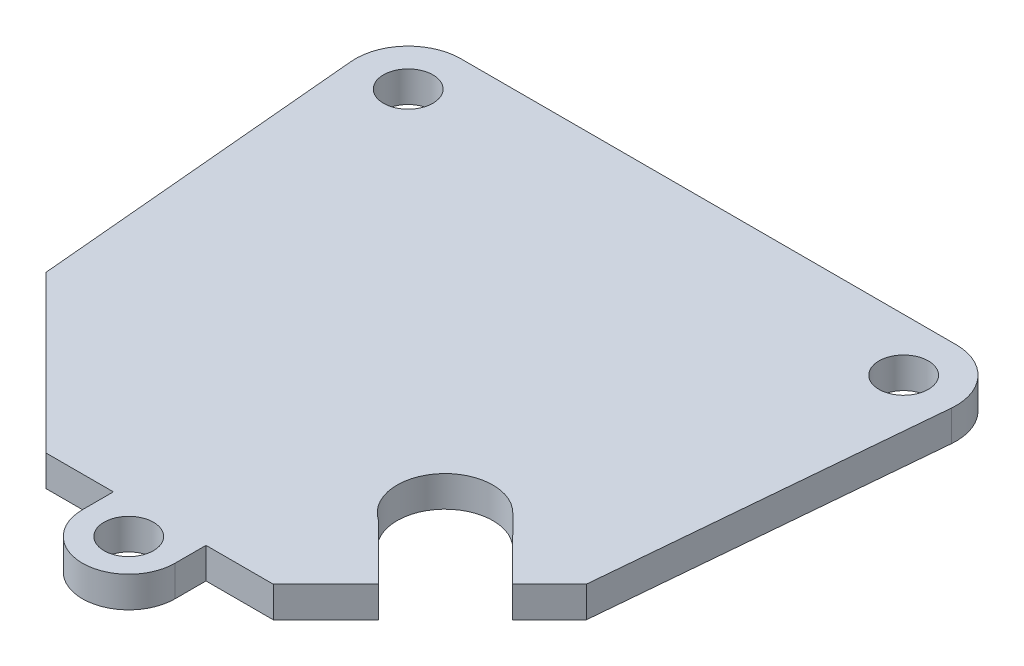
SolidWorks part; units mm, degrees
ref_plane "Front Plane" through (0, 0, 0) normal (0, 0, 1) x (1, 0, 0)
ref_plane "Top Plane" through (0, 0, 0) normal (0, 1, 0) x (1, 0, 0)
ref_plane "Right Plane" through (0, 0, 0) normal (1, 0, 0) x (0, 0, -1)
sketch "Sketch1" plane through (0, 0, 0) normal (0, 1, 0) x (1, 0, 0)
  line L0 (-0.5707, -3.253) -> (-0.5707, -1.2483)
  line L1 (-0.5707, -1.2483) -> (3.7934, -1.2483)
  line L2 (3.7934, -1.2483) -> (7.1926, 2.1509)
  line L3 (13.9293, 8.8876) -> (15.8745, 30.5956)
  line L4 (-21.0707, 8.8876) -> (-23.0159, 30.5956)
  line L5 (-10.9348, -1.2483) -> (-21.0707, 8.8876)
  line L6 (-6.5707, -1.2483) -> (-10.9348, -1.2483)
  line L7 (-6.5707, -3.253) -> (-6.5707, -1.2483)
  line L8 (12.4793, 34.3086) -> (-19.6207, 34.3086)
  line L9 (3.5655, 5.7781) -> (7.1926, 2.1509)
  line L10 (7.5366, 10.5201) -> (11.5457, 6.504)
  line L11 (11.5457, 6.504) -> (13.9293, 8.8876)
  circle A0 centre (-3.5707, -3.253) radius 1.6
  arc A1 (-6.5707, -3.253) -> (-0.5707, -3.253) centre (-3.5707, -3.253) ccw
  circle A2 centre (12.4793, 30.8998) radius 1.6
  circle A3 centre (-19.6207, 30.8998) radius 1.6
  arc A4 (15.8745, 30.5956) -> (12.4793, 34.3086) centre (12.4793, 30.8998) ccw
  arc A5 (-23.0159, 30.5956) -> (-19.6207, 34.3086) centre (-19.6207, 30.8998) cw
  circle A6 centre (-19.6207, 30.8998) radius 1.6
  arc A7 (7.5366, 10.5201) -> (3.5655, 5.7781) centre (5.3392, 8.3265) ccw
  point P25 (0, 0)
extrude "Boss-Extrude1" add sketch "Sketch1" along normal blind 2 contours A7 L10 L11 L3 A4 L8 A5 L4 L5 L6 L7 A1 L0 L1 L2 L9 A3 A2 A0
